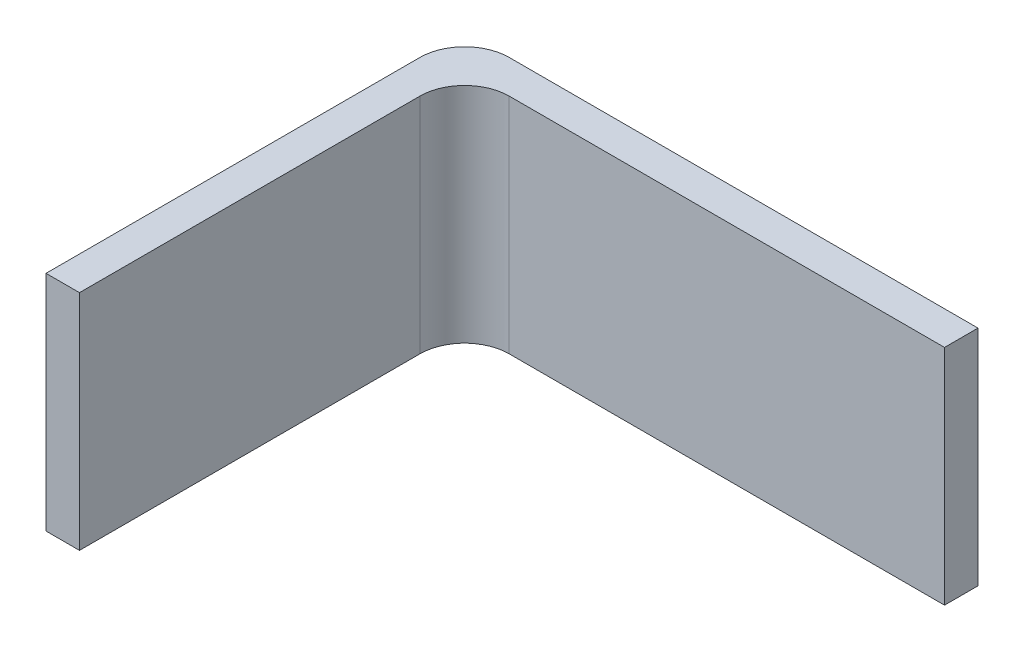
SolidWorks part; units mm, degrees
material "BUTYL"
ref_plane "前视基准面" through (0, 0, 0) normal (0, 0, 1) x (1, 0, 0)
ref_plane "上视基准面" through (0, 0, 0) normal (0, 1, 0) x (1, 0, 0)
ref_plane "右视基准面" through (0, 0, 0) normal (1, 0, 0) x (0, 0, -1)
sketch "草图1" plane through (0, 0, 0) normal (0, 1, 0) x (1, 0, 0)
  line L0 (0, -8) -> (0, -75)
  line L1 (8, 0) -> (92, 0)
  line L2 (92, 0) -> (92, -6)
  line L3 (92, -6) -> (14, -6)
  line L4 (6, -14) -> (6, -75)
  line L5 (6, -75) -> (0, -75)
  arc A0 (0, -8) -> (8, 0) centre (8, -8) cw
  arc A1 (14, -6) -> (6, -14) centre (14, -14) ccw
  point P9 (0, 0)
  dimension "D1" = 8
  dimension "D2" = 8
  dimension "D3" = 6
  dimension "D4" = 6
  dimension "D5" = 67
  dimension "D6" = 84
extrude "凸台-拉伸1" add sketch "草图1" along normal blind 40
